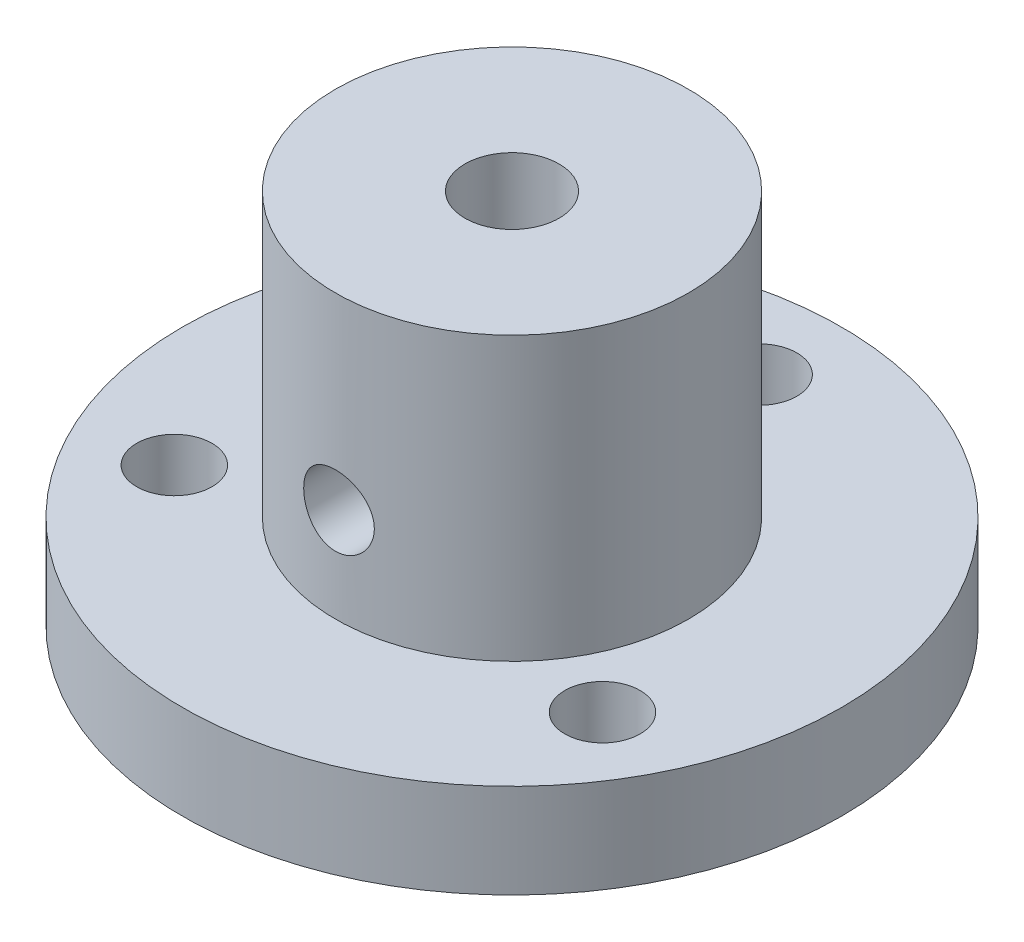
SolidWorks part; units mm, degrees
ref_plane "Front" through (0, 0, 0) normal (0, 0, 1) x (1, 0, 0)
ref_plane "Top" through (0, 0, 0) normal (0, 1, 0) x (1, 0, 0)
ref_plane "Right" through (0, 0, 0) normal (1, 0, 0) x (0, 0, -1)
sketch "Sketch1" plane through (0, 0, 0) normal (0, 0, 1) x (1, 0, 0)
  line L0 (-14, 0) -> (-14, 4)
  line L1 (-14, 4) -> (-7.5, 4)
  line L2 (-7.5, 4) -> (-7.5, 16)
  line L3 (-7.5, 16) -> (-2, 16)
  line L4 (-2, 16) -> (-2, 0)
  line L5 (-2, 0) -> (-14, 0)
  line L6 (0, 0) -> (0, -11.8055) construction
  point P7 (-7.5, 6.3657)
  point P10 (-3.5095, 0)
  dimension "D1" = 4
  dimension "D2" = 7.5
  dimension "D3" = 14
  dimension "D4" = 12
  dimension "D5" = 2
revolve "Revolve1" add sketch "Sketch1" angle 360 about L6
sketch "Sketch2" plane through (0, 0, 0) normal (0, 1, 0) x (1, 0, 0)
  line L0 (0, 10.5) -> (0, 0) construction
  line L1 (0, 10.5) -> (-9.0933, -5.25) construction
  line L2 (-9.0933, -5.25) -> (9.0933, -5.25) construction
  line L3 (9.0933, -5.25) -> (0, 10.5) construction
  line L4 (0, 0) -> (9.0933, -5.25) construction
  line L5 (0, 0) -> (-9.0933, -5.25) construction
  circle A0 centre (0, 10.5) radius 1.6
  circle A1 centre (9.0933, -5.25) radius 1.6
  circle A2 centre (-9.0933, -5.25) radius 1.6
  point P5 (9.0933, -5.25)
  dimension "D2" = 3.2
  dimension "D1" = 10.5
  dimension "D3" = 3
extrude "Cut-Extrude1" cut sketch "Sketch2" along normal through all
sketch "Sketch3" plane through (0, 0, 0) normal (0, 0, 1) x (1, 0, 0)
  line L0 (2, 16) -> (-2, 16) construction
  circle A0 centre (0, 8) radius 1.5
  point P4 (0, 0)
  dimension "D2" = 3
  dimension "D1" = 8
extrude "Cut-Extrude2" cut sketch "Sketch3" along normal through all
